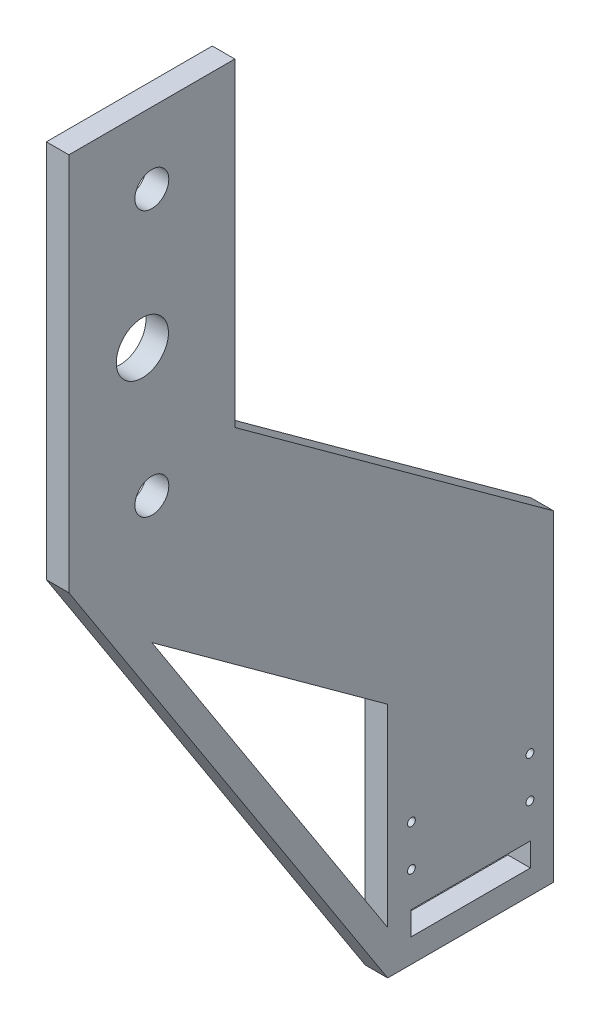
SolidWorks part; units mm, degrees
ref_plane "Front Plane" through (0, 0, 0) normal (0, 0, 1) x (1, 0, 0)
ref_plane "Top Plane" through (0, 0, 0) normal (0, 1, 0) x (1, 0, 0)
ref_plane "Right Plane" through (0, 0, 0) normal (1, 0, 0) x (0, 0, -1)
sketch "Sketch1" plane through (0, 0, 0) normal (1, 0, 0) x (0, 0, -1)
  line L0 (0, 0) -> (70, 0)
  line L1 (70, 0) -> (70, 135.6671)
  line L2 (70, 135.6671) -> (-64.5, 233.3855)
  line L3 (0, 18.4162) -> (0, 100)
  line L4 (0, 100) -> (-99.5, 172.2898)
  line L5 (-134.5, 208) -> (-134.5, 368)
  line L6 (-134.5, 368) -> (-64.5, 368)
  line L7 (-64.5, 368) -> (-64.5, 233.3855)
  line L8 (-99.5, 368) -> (-99.5, 172.2898) construction
  line L9 (-103.5, 282) -> (-114.5, 282) construction
  line L10 (-134.5, 208) -> (0, 0)
  line L11 (9.8, 20) -> (60.2, 20)
  line L12 (9.8, 20) -> (9.8, 10.1)
  line L13 (9.8, 10.1) -> (60.2, 10.1)
  line L14 (60.2, 20) -> (60.2, 10.1)
  line L15 (-99.5, 172.2898) -> (0, 18.4162)
  circle A0 centre (-99.5, 338) radius 7.15
  circle A1 centre (-99.5, 226) radius 7.15
  circle A2 centre (-103.5, 282) radius 11
  point P28 (35, 10.1)
  point P29 (35, 0)
  dimension "D6" = 112
  dimension "D7" = 14.3
  dimension "D8" = 30
  dimension "D9" = 22
  dimension "D15" = 70
  dimension "D2" = 368
  dimension "D3" = 204.5
  dimension "D4" = 70
  dimension "D5" = 70
  dimension "D10" = 4
  dimension "D11" = 50.4
  dimension "D12" = 9.9
  dimension "D13" = 20
  dimension "D16" = 160
  dimension "D17" = 100
  dimension "D18" = 10
extrude "Boss-Extrude1" add sketch "Sketch1" along normal blind 9.5
hole_wizard "M4 Tapped Hole1" positions "Sketch2" profile "Sketch3" tap size "M4" standard "ISO" end condition through all
sketch "Sketch2" plane through (9.5, 0, 0) normal (1, 0, 0) x (0, 0, -1)
  line L0 (60.2, 20) -> (9.8, 20) construction
  line L1 (35, 0) -> (35, 193.2078) construction
  line L2 (0, 0) -> (70, 0) construction
  point P0 (10, 34.7)
  point P2 (10, 52)
  point P15 (60, 34.7)
  point P16 (60, 52)
  dimension "D1" = 14.7
  dimension "D2" = 17.3
  dimension "D3" = 50
sketch "Sketch3" plane through (9.5, 34.7, -10) normal (0, 1, 0) x (0, 0, -1)
  line L0 (0, 0) -> (0, 9.5)
  line L1 (0, 9.5) -> (1.65, 9.5)
  line L2 (1.65, 9.5) -> (1.65, 0)
  line L5 (1.65, 0) -> (0, 0)
  line L11 (0, -6.35) -> (0, 107.95) construction
  dimension "Thru Tap Drill Dia." = 3.3
  dimension "Thru Tap Drill Depth" = 9.5
cosmetic thread "Hole Thread1" parameters "D2"=4
cosmetic thread "Hole Thread2" parameters "D2"=4
cosmetic thread "Hole Thread3" parameters "D2"=4
cosmetic thread "Hole Thread4" parameters "D2"=4
